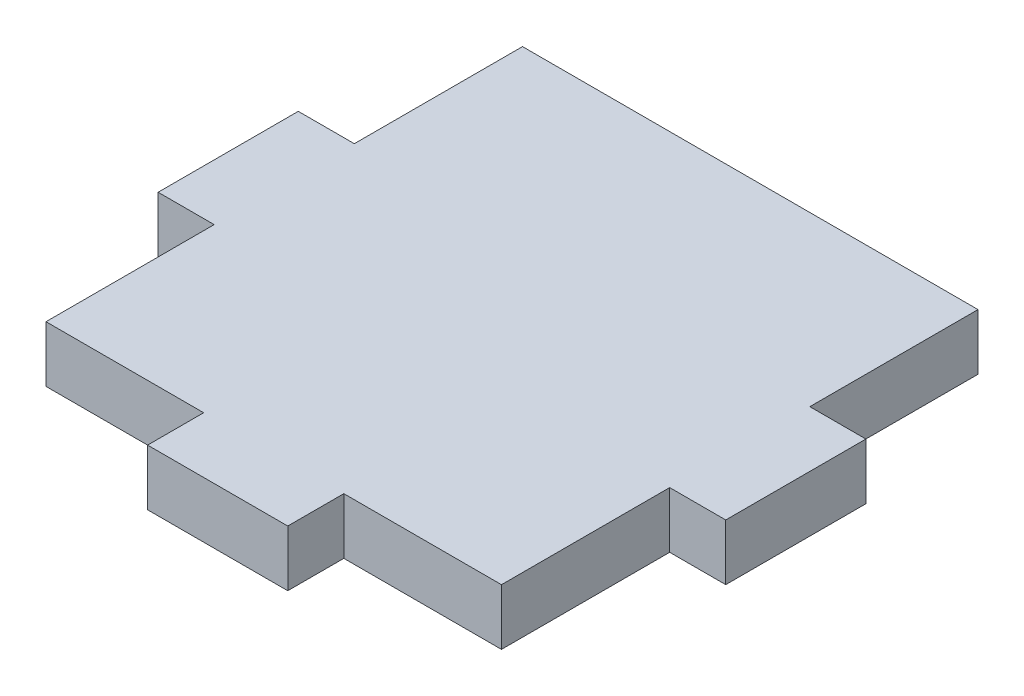
SolidWorks part; units mm, degrees
material "Maple"
ref_plane "Front Plane" through (0, 0, 0) normal (0, 0, 1) x (1, 0, 0)
ref_plane "Top Plane" through (0, 0, 0) normal (0, 1, 0) x (1, 0, 0)
ref_plane "Right Plane" through (0, 0, 0) normal (1, 0, 0) x (0, 0, -1)
sketch "Sketch1" plane through (0, 0, 0) normal (0, 1, 0) x (1, 0, 0)
  line L1 (0, 0) -> (32.5, 0)
  line L2 (0, 0) -> (0, -34)
  line L3 (0, -34) -> (32.5, -34)
  line L4 (32.5, 0) -> (32.5, -34)
  dimension "D1" = 32.5
  dimension "D2" = 34
extrude "Boss-Extrude1" add sketch "Sketch1" along normal blind 4
sketch "Sketch2" plane through (0, 0, 0) normal (0, -1, 0) x (1, 0, 0)
  line L0 (16.25, 34) -> (16.25, 0) construction
  line L1 (0, 34) -> (32.5, 34) construction
  line L2 (32.5, 0) -> (0, 0) construction
  line L3 (0, 17) -> (32.5, 17) construction
  line L4 (0, 0) -> (0, 34) construction
  line L5 (32.5, 34) -> (32.5, 0) construction
  line L7 (11.25, 38) -> (21.25, 38)
  line L8 (11.25, 38) -> (11.25, 34)
  line L9 (11.25, 34) -> (21.25, 34)
  line L10 (21.25, 38) -> (21.25, 34)
  line L11 (11.25, 38) -> (21.25, 34) construction
  line L12 (11.25, 34) -> (21.25, 38) construction
  line L13 (32.5, 22) -> (36.5, 22)
  line L14 (32.5, 22) -> (32.5, 12)
  line L15 (32.5, 12) -> (36.5, 12)
  line L16 (36.5, 22) -> (36.5, 12)
  line L17 (32.5, 22) -> (36.5, 12) construction
  line L18 (32.5, 12) -> (36.5, 22) construction
  line L19 (-4, 22) -> (0, 22)
  line L20 (-4, 22) -> (-4, 12)
  line L21 (-4, 12) -> (0, 12)
  line L22 (0, 22) -> (0, 12)
  line L23 (-4, 22) -> (0, 12) construction
  line L24 (-4, 12) -> (0, 22) construction
  point P12 (16.25, 36)
  point P17 (34.5, 17)
  point P22 (-2, 17)
  dimension "D1" = 4
  dimension "D2" = 10
extrude "Boss-Extrude2" add sketch "Sketch2" against normal through all
